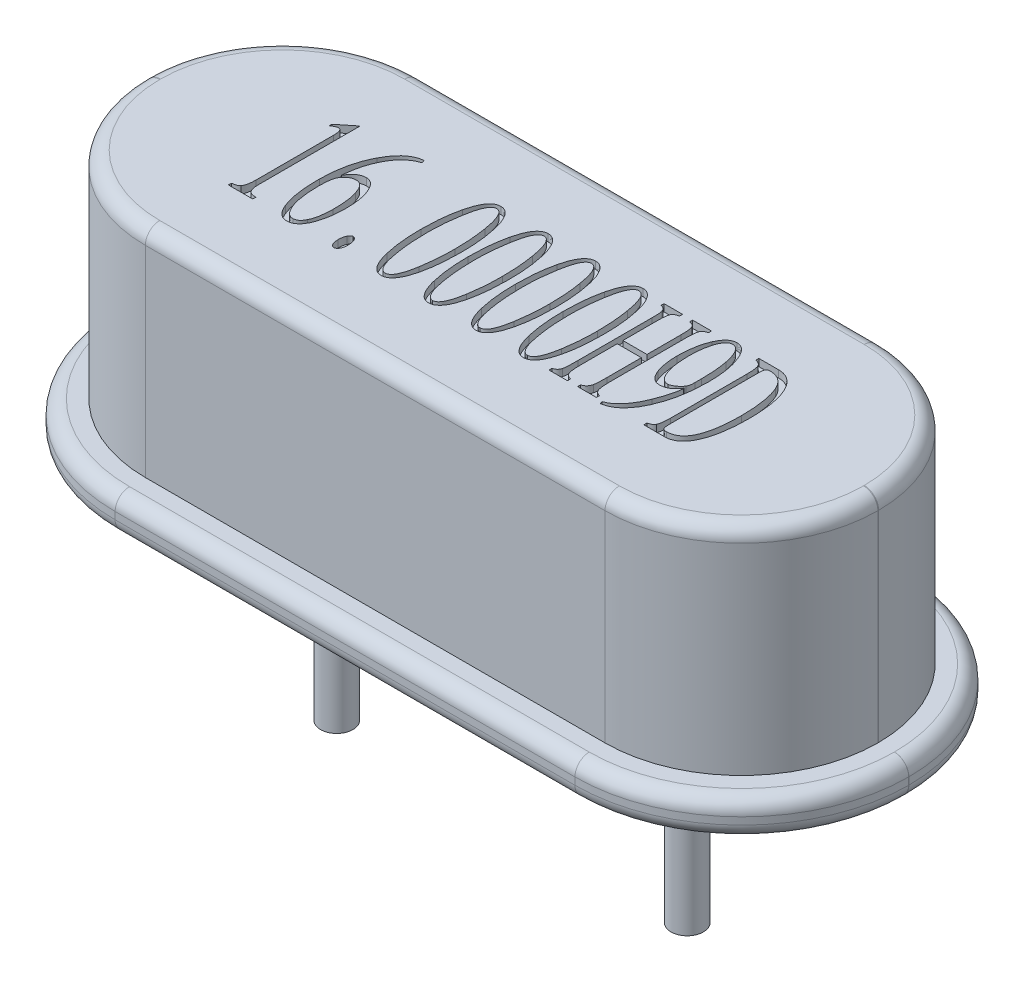
SolidWorks part; units mm, degrees
ref_plane "Front Plane" through (0, 0, 0) normal (0, 0, 1) x (1, 0, 0)
ref_plane "Top Plane" through (0, 0, 0) normal (0, 1, 0) x (1, 0, 0)
ref_plane "Right Plane" through (0, 0, 0) normal (1, 0, 0) x (0, 0, -1)
sketch "Sketch1" plane through (0, 0, 0) normal (0, 1, 0) x (1, 0, 0)
  line L1 (-3.201, -2.325) -> (3.201, -2.325)
  line L2 (-5.525, -0.001) -> (-5.525, 0.001)
  line L3 (-3.201, 2.325) -> (3.201, 2.325)
  line L4 (5.525, -0.001) -> (5.525, 0.001)
  line L5 (-5.525, -2.325) -> (5.525, 2.325) construction
  line L6 (-5.525, 2.325) -> (5.525, -2.325) construction
  arc A0 (3.201, 2.325) -> (5.525, 0.001) centre (3.201, 0.001) cw
  arc A1 (3.201, -2.325) -> (5.525, -0.001) centre (3.201, -0.001) ccw
  arc A2 (-3.201, -2.325) -> (-5.525, -0.001) centre (-3.201, -0.001) cw
  arc A3 (-5.525, 0.001) -> (-3.201, 2.325) centre (-3.201, 0.001) cw
  point P0 (0, 0)
  dimension "D3" = 2.324
  dimension "D1" = 4.65
  dimension "D2" = 11.05
extrude "Boss-Extrude1" add sketch "Sketch1" along normal blind 0.5
sketch "Sketch2" plane through (0, 0.5, 0) normal (0, 1, 0) x (1, 0, 0)
  line L1 (-3.2, -1.905) -> (3.2, -1.905)
  line L2 (-5.1, -0.005) -> (-5.1, 0.005)
  line L3 (-3.2, 1.905) -> (3.2, 1.905)
  line L4 (5.1, -0.005) -> (5.1, 0.005)
  line L5 (-5.1, -1.905) -> (5.1, 1.905) construction
  line L6 (-5.1, 1.905) -> (5.1, -1.905) construction
  arc A0 (3.2, 1.905) -> (5.1, 0.005) centre (3.2, 0.005) cw
  arc A1 (3.2, -1.905) -> (5.1, -0.005) centre (3.2, -0.005) ccw
  arc A2 (-3.2, -1.905) -> (-5.1, -0.005) centre (-3.2, -0.005) cw
  arc A3 (-5.1, 0.005) -> (-3.2, 1.905) centre (-3.2, 0.005) cw
  point P0 (0, 0)
  dimension "D3" = 1.9
  dimension "D1" = 3.81
  dimension "D2" = 10.2
extrude "Boss-Extrude2" add sketch "Sketch2" along normal blind 3
fillet "Fillet1" radius 0.2 24 edges at (-4.8443, 0, 1.6443) (-5.525, 0, 0) (-4.8443, 0, -1.6443) (0, 0, -2.325) (4.8443, 0, -1.6443) (5.525, 0, 0) (4.8443, 0, 1.6443) (-4.8443, 0.5, 1.6443) (-5.525, 0.5, 0) (-4.8443, 0.5, -1.6443) (0, 0.5, -2.325) (4.8443, 0.5, -1.6443) (5.525, 0.5, 0) (4.8443, 0.5, 1.6443) (-4.5435, 3.5, 1.3485) (-5.1, 3.5, 0) (-4.5435, 3.5, -1.3485) (0, 3.5, -1.905) (4.5435, 3.5, -1.3485) (5.1, 3.5, 0) (4.5435, 3.5, 1.3485) (0, 0, 2.325) (0, 0.5, 2.325) (0, 3.5, 1.905)
sketch "Sketch3" plane through (0, 0, 0) normal (0, -1, 0) x (1, 0, 0)
  circle A0 centre (-2.44, 0) radius 0.225
  circle A1 centre (2.44, 0) radius 0.225
  dimension "D2" = 0.45
  dimension "D4" = 0.45
  dimension "D1" = 2.44
  dimension "D3" = 2.44
extrude "Boss-Extrude3" add sketch "Sketch3" along normal blind 3
sketch "Sketch4" plane through (0, 3.5, 0) normal (0, 1, 0) x (1, 0, 0)
  text T0 "16.0000H9D" font "@MingLiU_HKSCS-ExtB" height 1.6
extrude "Cut-Extrude1" cut sketch "Sketch4" against normal blind 0.1
